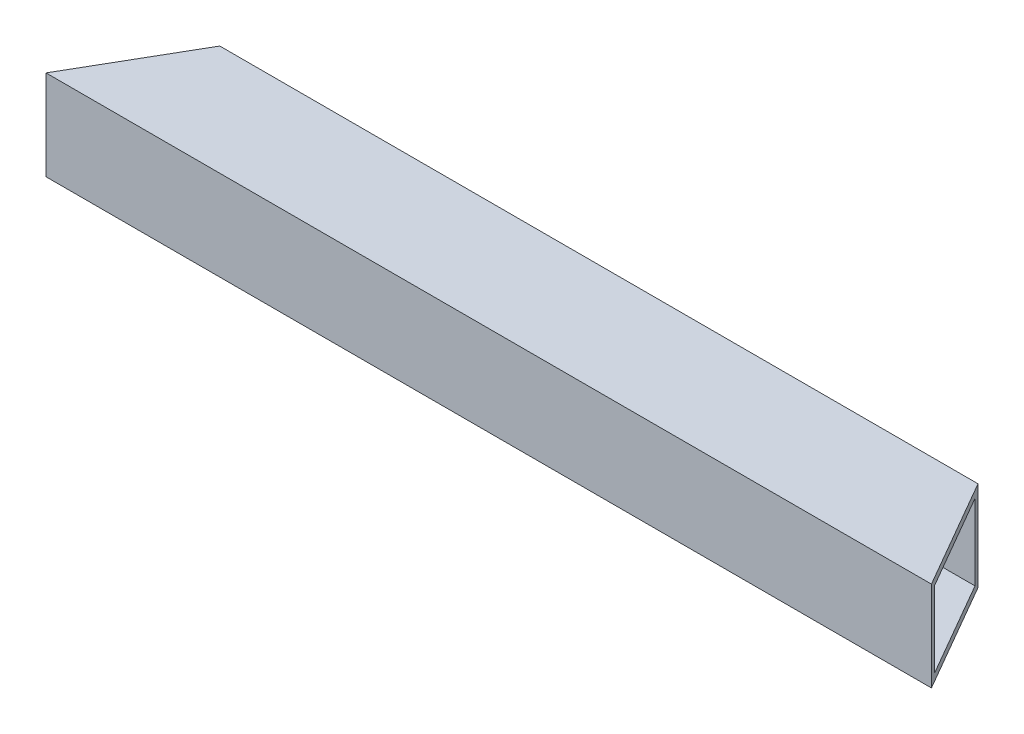
SolidWorks part; units mm, degrees
ref_plane "Front Plane" through (0, 0, 0) normal (0, 0, 1) x (1, 0, 0)
ref_plane "Top Plane" through (0, 0, 0) normal (0, 1, 0) x (1, 0, 0)
ref_plane "Right Plane" through (0, 0, 0) normal (1, 0, 0) x (0, 0, -1)
sketch "Sketch1" plane through (0, 0, 0) normal (0, 1, 0) x (1, 0, 0)
  line L0 (-90.5561, -9.2081) -> (-72.5956, 21.9005)
  line L1 (-72.5956, 21.9005) -> (141.4834, 21.9005)
  line L2 (159.4439, -9.2081) -> (141.4834, 21.9005)
  line L3 (-90.5561, -9.2081) -> (159.4439, -9.2081)
  dimension "D1" = 60
  dimension "D3" = 60
extrude "Boss-Extrude1" add sketch "Sketch1" along normal blind 25.4
shell "Shell3" thickness 2
